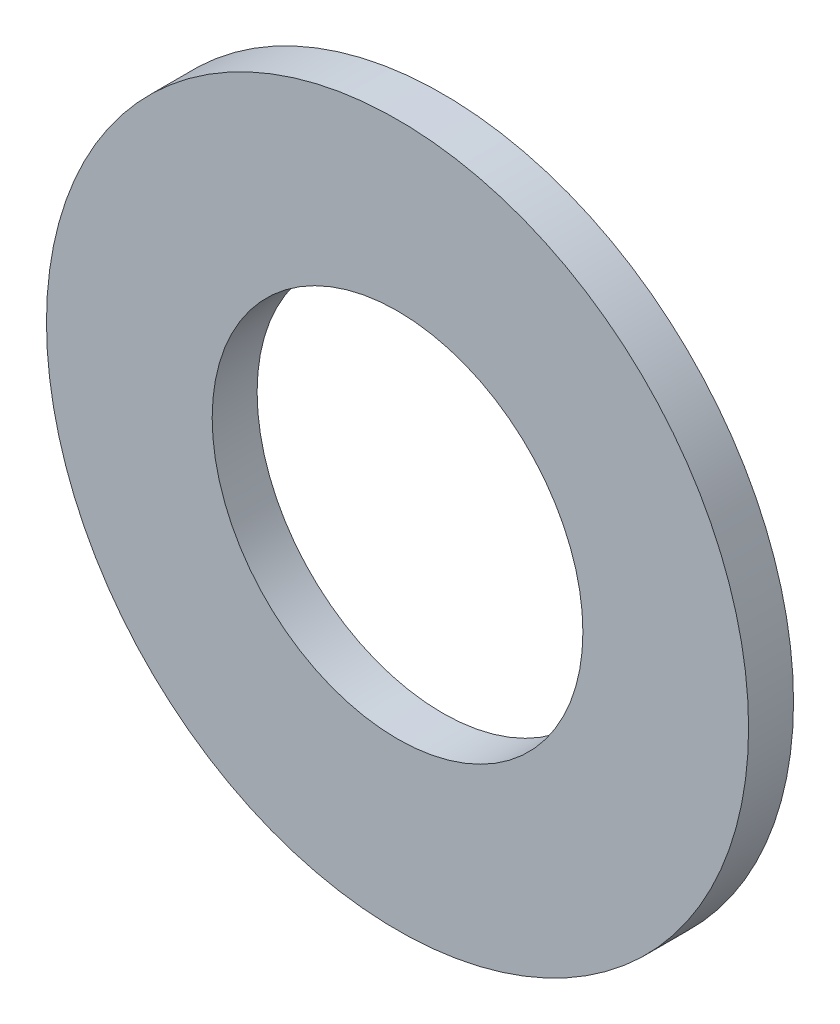
SolidWorks part; units mm, degrees
material "6061-T6 (SS)"
ref_plane "Top" through (0, 0, 0) normal (0, 0, 1) x (1, 0, 0)
ref_plane "Right" through (0, 0, 0) normal (0, 1, 0) x (1, 0, 0)
ref_plane "Front" through (0, 0, 0) normal (1, 0, 0) x (0, 0, -1)
sketch "Sketch1" plane through (0, 0, 0) normal (0, 0, 1) x (1, 0, 0)
  circle A0 centre (0, 0) radius 6.35
  circle A1 centre (0, 0) radius 3.3528
  dimension "D1" = 6.7056
  dimension "D2" = 12.7
extrude "Boss-Extrude1" add sketch "Sketch1" along normal blind 0.8128
move or copy body "Body-Move/Copy1" [suppressed] bodies to move or copy 101
